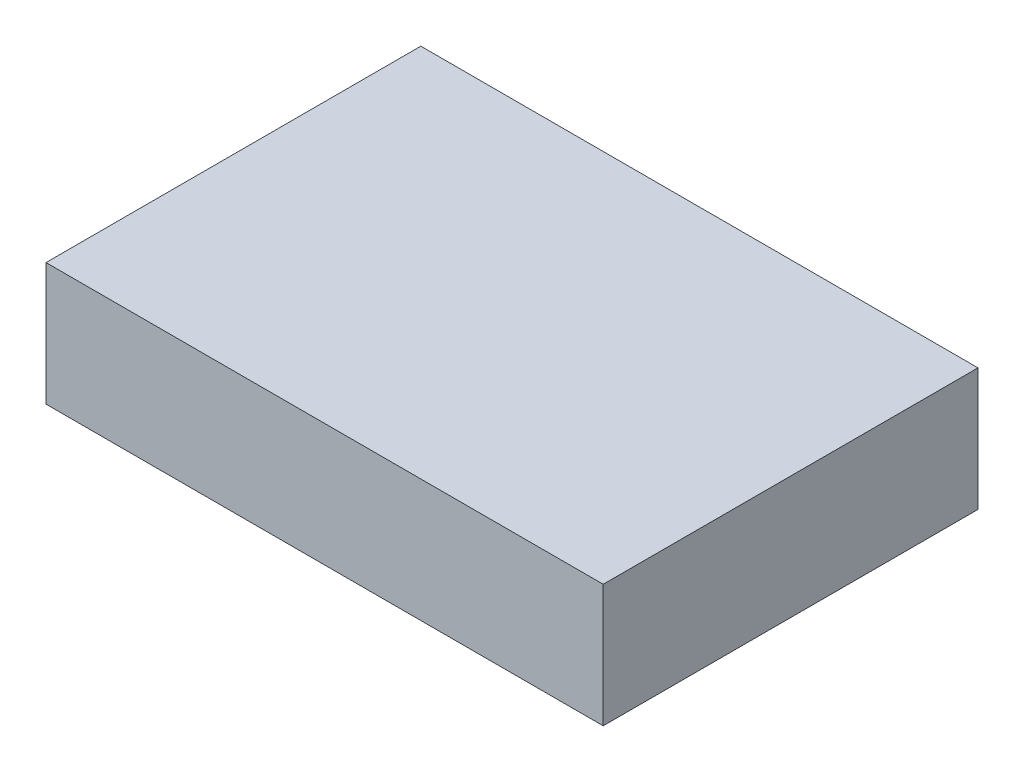
SolidWorks part; units mm, degrees
ref_plane "Front Plane" through (0, 0, 0) normal (0, 0, 1) x (1, 0, 0)
ref_plane "Top Plane" through (0, 0, 0) normal (0, 1, 0) x (1, 0, 0)
ref_plane "Right Plane" through (0, 0, 0) normal (1, 0, 0) x (0, 0, -1)
other "Graphic1"
sketch "Sketch1" plane through (0, 0, 0) normal (0, 1, 0) x (1, 0, 0)
  line L1 (-312.706, 132.0167) -> (-185.006, 132.0167)
  line L2 (-312.706, 132.0167) -> (-312.706, 46.1167)
  line L3 (-312.706, 46.1167) -> (-185.006, 46.1167)
  line L4 (-185.006, 132.0167) -> (-185.006, 46.1167)
  dimension "D1" = 85.9
  dimension "D2" = 127.7
extrude "Boss-Extrude1" add sketch "Sketch1" along normal blind 28.1
